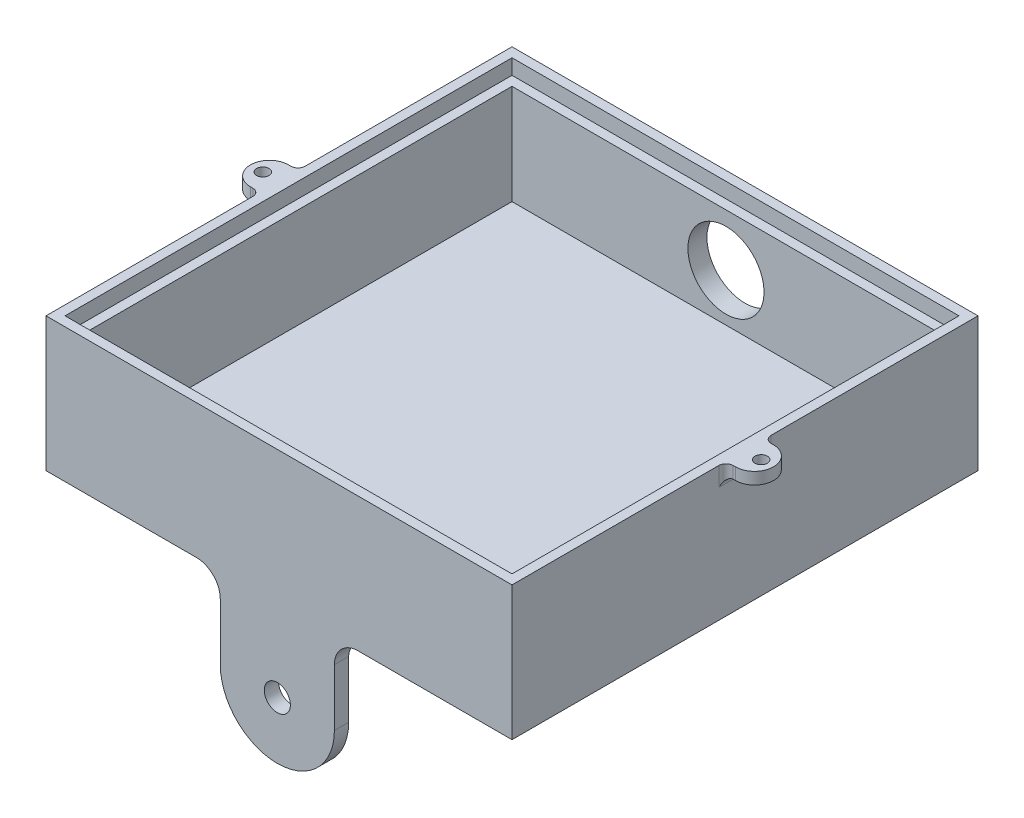
SolidWorks part; units mm, degrees
ref_plane "Front Plane" through (0, 0, 0) normal (0, 0, 1) x (1, 0, 0)
ref_plane "Top Plane" through (0, 0, 0) normal (0, 1, 0) x (1, 0, 0)
ref_plane "Right Plane" through (0, 0, 0) normal (1, 0, 0) x (0, 0, -1)
sketch "Sketch1" plane through (0, 0, 0) normal (0, 1, 0) x (1, 0, 0)
  line L1 (-49, 49) -> (49, 49)
  line L2 (-49, 49) -> (-49, -49)
  line L3 (-49, -49) -> (49, -49)
  line L4 (49, 49) -> (49, -49)
  line L5 (-49, 49) -> (49, -49) construction
  line L6 (-49, -49) -> (49, 49) construction
  point P0 (0, 0)
  dimension "D1" = 98
  dimension "D2" = 98
extrude "Boss-Extrude1" add sketch "Sketch1" along normal blind 30
sketch "Sketch2" plane through (0, 30, 0) normal (0, 1, 0) x (1, 0, 0)
  line L1 (-47, 47) -> (47, 47)
  line L2 (-47, 47) -> (-47, -47)
  line L3 (-47, -47) -> (47, -47)
  line L4 (47, 47) -> (47, -47)
  line L5 (-47, 47) -> (47, -47) construction
  line L6 (-47, -47) -> (47, 47) construction
  point P0 (0, 0)
  dimension "D1" = 94
  dimension "D2" = 94
extrude "Cut-Extrude1" cut sketch "Sketch2" against normal blind 5
sketch "Sketch3" plane through (0, 25, 0) normal (0, 1, 0) x (1, 0, 0)
  line L1 (-45, 45) -> (45, 45)
  line L2 (-45, 45) -> (-45, -45)
  line L3 (-45, -45) -> (45, -45)
  line L4 (45, 45) -> (45, -45)
  line L5 (-45, 45) -> (45, -45) construction
  line L6 (-45, -45) -> (45, 45) construction
  point P0 (0, 0)
  dimension "D1" = 90
  dimension "D2" = 90
extrude "Cut-Extrude2" cut sketch "Sketch3" against normal blind 21
sketch "Sketch4" plane through (0, 30, 0) normal (0, 1, 0) x (1, 0, 0)
  line L1 (-47, 47) -> (47, 47)
  line L2 (-47, 47) -> (-47, -47)
  line L3 (-47, -47) -> (47, -47)
  line L4 (47, 47) -> (47, -47)
  line L5 (-49, 49) -> (49, 49)
  line L6 (-49, 49) -> (-49, -49)
  line L7 (-49, -49) -> (49, -49)
  line L8 (49, 49) -> (49, -49)
extrude "Cut-Extrude3" cut sketch "Sketch4" against normal blind 1.8
sketch "Sketch5" plane through (0, 28.2, 0) normal (0, 1, 0) x (1, 0, 0)
  line L0 (-49, 49) -> (-49, -49) construction
  line L1 (-49, 4) -> (-51, 4)
  line L2 (-49, 4) -> (-49, -4)
  line L3 (-49, -4) -> (-51, -4)
  line L5 (49, 49) -> (-49, 49) construction
  line L7 (0, -8.1636) -> (0, 15.1829) construction
  line L8 (49, 4) -> (49, -4)
  line L9 (49, -4) -> (51, -4)
  line L10 (49, 4) -> (51, 4)
  arc A0 (-51, 4) -> (-51, -4) centre (-51, 0) ccw
  circle A1 centre (-52.4, 0) radius 1.3
  circle A2 centre (52.4, 0) radius 1.3
  arc A3 (51, 4) -> (51, -4) centre (51, 0) cw
  dimension "D4" = 2.6
  dimension "D1" = 2
  dimension "D2" = 8
  dimension "D3" = 45
  dimension "D5" = 3.4
extrude "Boss-Extrude2" add sketch "Sketch5" against normal blind 2.5
fillet "Fillet1" radius 1.5 3 edges at (-49, 26.95, -4) (-49, 25.7, 0) (-49, 26.95, 4)
fillet "Fillet2" radius 1.5 3 edges at (49, 26.95, -4) (49, 25.7, 0) (49, 26.95, 4)
sketch "Sketch6" plane through (0, 0, -49) normal (0, 0, -1) x (-1, 0, 0)
  line L0 (-49, 0) -> (49, 0) construction
  circle A0 centre (0, 14) radius 8
  dimension "D1" = 16
  dimension "D2" = 14
extrude "Cut-Extrude4" cut sketch "Sketch6" against normal up to next
sketch "Sketch7" plane through (0, 0, 0) normal (0, -1, 0) x (1, 0, 0)
  line L3 (-4, -10) -> (-1, -10)
  line L6 (-4, 10) -> (1, 10)
  line L7 (-1, -10) -> (1, -10)
  line L8 (-4, 10) -> (-4, -10)
  line L9 (-49, -49) -> (-49, 49) construction
  arc A0 (1, 0) -> (1, 10) centre (1, 5) ccw
  arc A1 (1, -10) -> (1, 0) centre (1, -5) ccw
  circle A2 centre (1, 5) radius 1.9684
  circle A3 centre (1, -5) radius 1.9684
  dimension "D4" = 10
  dimension "D6" = 10
  dimension "D7" = 5
  dimension "D11" = 3.9367
  dimension "D3" = 45
  dimension "D12" = 5
extrude "Cut-Extrude5" cut sketch "Sketch7" against normal blind 1
sketch "Sketch8" plane through (0, 0, 49) normal (0, 0, 1) x (1, 0, 0)
  line L0 (-49, 0) -> (49, 0) construction
  line L2 (11.6486, -17) -> (11.6486, 0)
  line L3 (11.6486, 0) -> (-12.3514, 0)
  line L4 (-12.3514, -17) -> (-12.3514, 0)
  arc A0 (-12.3514, -17) -> (11.6486, -17) centre (-0.3514, -17) ccw
  circle A1 centre (-0.3514, -17) radius 2.75
  point P0 (-0.3514, -8.5)
  dimension "D3" = 5.5
  dimension "D1" = 24
  dimension "D2" = 17
extrude "Boss-Extrude3" add sketch "Sketch8" against normal blind 3
fillet "Fillet3" radius 5 3 edges at (-12.3514, 0, 47.5) (11.6486, 0, 47.5) (-0.3514, 0, 46)
